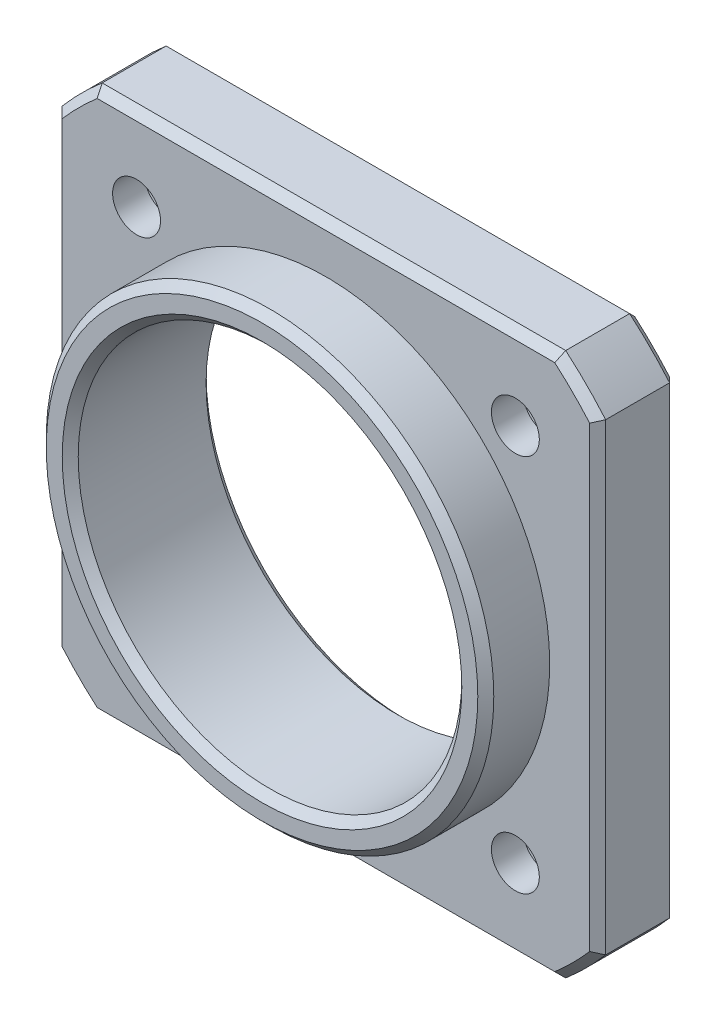
SolidWorks part; units mm, degrees
material "1060 Alloy"
ref_plane "Front Plane" through (0, 0, 0) normal (0, 0, 1) x (1, 0, 0)
ref_plane "Top Plane" through (0, 0, 0) normal (0, 1, 0) x (1, 0, 0)
ref_plane "Right Plane" through (0, 0, 0) normal (1, 0, 0) x (0, 0, -1)
sketch "Sketch1" plane through (0, 0, 0) normal (0, 0, 1) x (1, 0, 0)
  line L0 (-14.5, 17) -> (14.5, 17)
  line L1 (-17, 17) -> (17, 17) construction
  line L2 (-17, 17) -> (-17, -17) construction
  line L3 (-17, -17) -> (17, -17) construction
  line L4 (17, 17) -> (17, -17) construction
  line L5 (-17, 17) -> (17, -17) construction
  line L6 (-17, -17) -> (17, 17) construction
  line L7 (-11.85, 0) -> (11.85, 0) construction
  line L8 (17, -14.5) -> (17, 14.5)
  line L9 (14.5, -17) -> (-14.5, -17)
  line L10 (-17, 14.5) -> (-17, -14.5)
  line L11 (11.85, -11.85) -> (-11.85, -11.85) construction
  line L12 (11.85, -11.85) -> (11.85, 11.85) construction
  line L13 (11.85, 11.85) -> (-11.85, 11.85) construction
  line L14 (-11.85, -11.85) -> (-11.85, 11.85) construction
  line L15 (11.85, -11.85) -> (-11.85, 11.85) construction
  line L16 (11.85, 11.85) -> (-11.85, -11.85) construction
  line L17 (0, 11.85) -> (0, -11.85) construction
  circle A0 centre (0, 0) radius 22.3439 construction
  arc A1 (-17, -14.5) -> (-14.5, -17) centre (0, 0) ccw
  arc A2 (-14.5, 17) -> (-17, 14.5) centre (0, 0) ccw
  arc A3 (17, 14.5) -> (14.5, 17) centre (0, 0) ccw
  arc A4 (14.5, -17) -> (17, -14.5) centre (0, 0) ccw
  circle A5 centre (-11.85, 11.85) radius 1.5
  circle A6 centre (11.85, 11.85) radius 1.5
  circle A7 centre (11.85, -11.85) radius 1.5
  circle A8 centre (-11.85, -11.85) radius 1.5
  circle A9 centre (0, 0) radius 12
  point P9 (0, 17)
  dimension "D2" = 23.7
  dimension "D4" = 3
  dimension "D5" = 24
  dimension "D1" = 34
  dimension "D3" = 29
extrude "Boss-Extrude1" add sketch "Sketch1" along normal blind 9
sketch "Sketch2" plane through (0, 0, 9) normal (0, 0, 1) x (1, 0, 0)
  line L1 (-14.5, 17) -> (14.5, 17)
  line L2 (-17, 14.5) -> (-17, -14.5)
  line L3 (-14.5, -17) -> (14.5, -17)
  line L4 (17, 14.5) -> (17, -14.5)
  line L5 (-17, 17) -> (17, -17) construction
  line L6 (-17, -17) -> (17, 17) construction
  arc A0 (-17, -14.5) -> (-14.5, -17) centre (0, 0) ccw
  arc A1 (-14.5, 17) -> (-17, 14.5) centre (0, 0) ccw
  arc A2 (17, 14.5) -> (14.5, 17) centre (0, 0) ccw
  arc A3 (14.5, -17) -> (17, -14.5) centre (0, 0) ccw
  circle A4 centre (0, 0) radius 14
  dimension "D2" = 28
  dimension "D1" = 34
extrude "Cut-Extrude1" cut sketch "Sketch2" against normal blind 4
sketch "Sketch3" plane through (0, 0, 0) normal (0, 0, -1) x (-1, 0, 0)
  line L0 (-11.85, 0) -> (11.85, 0) construction
  line L1 (-11.85, -11.85) -> (11.85, -11.85) construction
  line L2 (-11.85, -11.85) -> (-11.85, 11.85) construction
  line L3 (-11.85, 11.85) -> (11.85, 11.85) construction
  line L4 (11.85, -11.85) -> (11.85, 11.85) construction
  line L5 (-11.85, -11.85) -> (11.85, 11.85) construction
  line L6 (-11.85, 11.85) -> (11.85, -11.85) construction
  line L7 (0, 11.85) -> (0, -11.85) construction
  circle A0 centre (-11.85, 11.85) radius 4
  circle A1 centre (11.85, 11.85) radius 4
  circle A2 centre (11.85, -11.85) radius 4
  circle A3 centre (-11.85, -11.85) radius 4
  point P0 (0, 0)
  dimension "D1" = 8
extrude "Cut-Extrude2" cut sketch "Sketch3" against normal blind 3
chamfer "Chamfer1" distance 0.5 angle 45 16 edges at (15.7995, -15.7995, 5) (0, -17, 5) (-15.7995, -15.7995, 5) (-17, 0, 5) (-15.7995, 15.7995, 5) (0, 17, 5) (15.7995, 15.7995, 5) (17, 0, 5) (15.7995, -15.7995, 0) (0, -17, 0) (-15.7995, -15.7995, 0) (-17, 0, 0) (-15.7995, 15.7995, 0) (0, 17, 0) (15.7995, 15.7995, 0) (17, 0, 0)
chamfer "Chamfer2" distance 0.5 angle 45 3 edges at (14, 0, 9) (12, 0, 9) (12, 0, 0)
